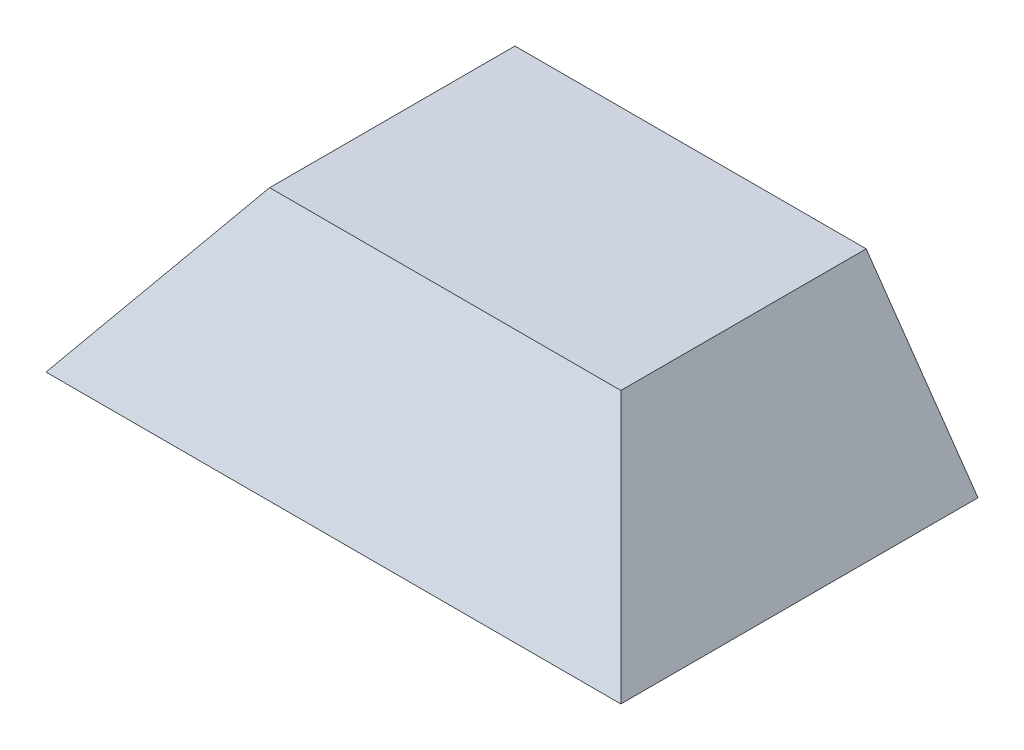
SolidWorks part; units mm, degrees
ref_plane "Alzado" through (0, 0, 0) normal (0, 0, 1) x (1, 0, 0)
ref_plane "Planta" through (0, 0, 0) normal (0, 1, 0) x (1, 0, 0)
ref_plane "Vista lateral" through (0, 0, 0) normal (1, 0, 0) x (0, 0, -1)
sketch "Croquis1" plane through (0, 0, 0) normal (0, 1, 0) x (1, 0, 0)
  line L1 (90, -64.665) -> (-90, -64.665)
  line L2 (90, -64.665) -> (90, 64.665)
  line L3 (90, 64.665) -> (-90, 64.665)
  line L4 (-90, -64.665) -> (-90, 64.665)
  line L5 (90, -64.665) -> (-90, 64.665) construction
  line L6 (90, 64.665) -> (-90, -64.665) construction
  point P0 (0, 0)
  dimension "D1" = 129.33
  dimension "D2" = 180
extrude "Saliente-Extruir1" add sketch "Croquis1" along normal blind 50
sketch "Croquis2" plane through (0, 0, 64.665) normal (0, 0, 1) x (1, 0, 0)
  line L0 (90, 0) -> (54.9896, 50)
  line L1 (-90, 50) -> (90, 50) construction
  line L2 (54.9896, 50) -> (90, 50)
  line L3 (90, 50) -> (90, 0)
  dimension "D1" = 35
extrude "Cortar-Extruir1" cut sketch "Croquis2" against normal up to next
sketch "Croquis4" plane through (-90, 0, 0) normal (-1, 0, 0) x (0, 0, 1)
  line L0 (-64.665, 0) -> (-29.6546, 50)
  line L1 (-64.665, 50) -> (64.665, 50) construction
  line L2 (-29.6546, 50) -> (-64.665, 50)
  line L3 (-64.665, 50) -> (-64.665, 0)
  dimension "D1" = 35
extrude "Cortar-Extruir2" cut sketch "Croquis4" against normal up to next
mirror "Simetría2" about plane through (0, 0, 0) normal (0, 0, 1) of "Cortar-Extruir2"
mirror "Simetría1" about plane through (0, 0, 0) normal (1, 0, 0) of "Cortar-Extruir1" second plane through (0, 0, 0) second plane normal (0, 0, 1)
shell "Vaciado1" thickness 4
sketch "Croquis7" plane through (0, 14.7644, 0) normal (0, 0, -1) x (-1, 0, 0)
  line L0 (-54.9896, 10.2356) -> (-72.4948, 10.2356)
  line L1 (-54.9896, 35.2356) -> (54.9896, 35.2356)
  line L3 (-54.9896, 10.2356) -> (54.9896, 10.2356)
  line L5 (-54.9896, 35.2356) -> (54.9896, 10.2356) construction
  line L6 (-54.9896, 10.2356) -> (54.9896, 35.2356) construction
  line L7 (-54.9896, 35.2356) -> (-90, -14.7644) construction
  line L8 (-72.4948, 10.2356) -> (-54.9896, 35.2356)
  line L9 (54.9896, 10.2356) -> (72.4948, 10.2356)
  line L10 (90, -14.7644) -> (54.9896, 35.2356) construction
  line L11 (72.4948, 10.2356) -> (54.9896, 35.2356)
  point P4 (0, 22.7356)
  dimension "D1" = 25
extrude "Saliente-Extruir4" add sketch "Croquis7" along normal offset from surface (102.5762 mm away) 10
sketch "Croquis14" plane through (0, 0, 0) normal (0, 0, 1) x (1, 0, 0)
  line L0 (-85.1169, 0) -> (-52.8799, 46.0392)
  line L1 (-52.8799, 46.0392) -> (52.9344, 46.0392)
  line L2 (52.9344, 46.0392) -> (85.1169, 0)
  line L3 (85.1169, 0) -> (-85.1169, 0)
extrude "Cortar-Extruir10" cut sketch "Croquis14" against normal offset from surface (92.5762 mm away) 10 up to face at (0, 37.5, -102.5762)
sketch "Croquis15" plane through (0, 0, 0) normal (1, 0, 0) x (0, 0, -1)
  line L0 (47.1598, 0) -> (47.1598, 50)
  line L1 (102.5762, 50) -> (-29.6546, 50) construction
  line L2 (47.1598, 50) -> (102.5762, 50)
  line L3 (102.5762, 50) -> (102.5762, 0)
  line L4 (61.5036, 0) -> (-61.5036, 0) construction
  line L5 (102.5762, 0) -> (47.1598, 0)
extrude "Cortar-Extruir11" cut sketch "Croquis15" against normal through all both and the other way through all
ref_plane "Plano1" through (70, 0, 0) normal (1, 0, 0) x (0, 0, -1)
sketch "Croquis19" plane through (70, 0, 0) normal (1, 0, 0) x (0, 0, -1)
  line L0 (47.1598, 0) -> (0, 0) construction
  line L1 (8.2963, 0) -> (-11.7037, 0)
  line L2 (8.2963, 0) -> (8.2963, 20)
  line L3 (8.2963, 20) -> (-11.7037, 20)
  line L4 (-11.7037, 0) -> (-11.7037, 20)
  line L5 (8.2963, 0) -> (-11.7037, 20) construction
  line L6 (8.2963, 20) -> (-11.7037, 0) construction
  point P4 (-1.7037, 10)
  dimension "D1" = 20
  dimension "D2" = 20
extrude "Saliente-Extruir6" add sketch "Croquis19" along normal up to next
sketch "Croquis20" plane through (70, 0, 0) normal (-1, 0, 0) x (0, 0, 1)
  line L0 (-8.2963, 0) -> (-8.2963, 20) construction
  line L1 (-8.2963, 10) -> (11.7037, 10)
  line L2 (-8.2963, 10) -> (-8.2963, 5)
  line L3 (-8.2963, 5) -> (11.7037, 5)
  line L4 (11.7037, 10) -> (11.7037, 5)
  line L5 (-8.2963, 10) -> (11.7037, 5) construction
  line L6 (-8.2963, 5) -> (11.7037, 10) construction
  line L7 (11.7037, 0) -> (11.7037, 20) construction
  point P4 (1.7037, 7.5)
  dimension "D1" = 5
extrude "Cortar-Extruir14" cut sketch "Croquis20" against normal blind 8
sketch "Croquis22" plane through (0, 5, 0) normal (0, 1, 0) x (1, 0, 0)
  line L0 (78, -1.7037) -> (70, -1.7037) construction
  line L1 (78, 8.2963) -> (78, -11.7037) construction
  line L2 (70, -27.5) -> (70, 27.5) construction
  circle A0 centre (74, -1.7037) radius 1.585
  dimension "D1" = 3.17
extrude "Cortar-Extruir15" cut sketch "Croquis22" against normal up to next
mirror "Simetría3" about plane through (0, 0, 0) normal (1, 0, 0) of "Cortar-Extruir15", "Cortar-Extruir14", "Saliente-Extruir6"
